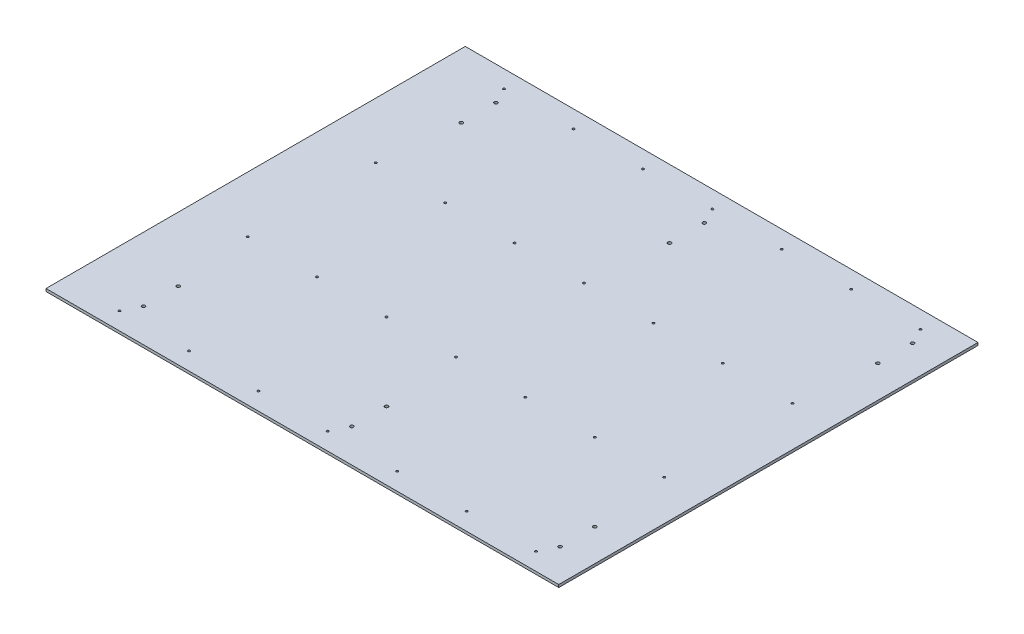
SolidWorks part; units mm, degrees
material "PC High Viscosity"
ref_plane "Front Plane" through (0, 0, 0) normal (0, 0, 1) x (1, 0, 0)
ref_plane "Top Plane" through (0, 0, 0) normal (0, 1, 0) x (1, 0, 0)
ref_plane "Right Plane" through (0, 0, 0) normal (1, 0, 0) x (0, 0, -1)
sketch "Sketch1" plane through (0, 0, 0) normal (0, 1, 0) x (1, 0, 0)
  line L1 (609.6, -498.475) -> (-609.6, -498.475)
  line L2 (609.6, -498.475) -> (609.6, 498.475)
  line L3 (609.6, 498.475) -> (-609.6, 498.475)
  line L4 (-609.6, -498.475) -> (-609.6, 498.475)
  line L5 (609.6, -498.475) -> (-609.6, 498.475) construction
  line L6 (609.6, 498.475) -> (-609.6, -498.475) construction
  point P0 (0, 0)
  dimension "D1" = 1219.2
  dimension "D2" = 996.95
extrude "Boss-Extrude1" add sketch "Sketch1" along normal blind 6.35
hole_wizard "13/64 (0.20313) Diameter Hole1" positions "Sketch2" profile "Sketch3" hole size "13/64" standard "ANSI Inch" end condition through all
sketch "Sketch2" plane through (0, 6.35, 0) normal (0, 1, 0) x (1, 0, 0)
  line L1 (-609.6, -498.475) -> (609.6, -498.475) construction
  line L2 (609.6, -498.475) -> (609.6, 498.475) construction
  point P0 (514.35, -457.2)
  dimension "D1" = 95.25
  dimension "D2" = 41.275
sketch "Sketch3" plane through (514.35, 6.35, 457.2) normal (1, 0, 0) x (0, 0, 1)
  line L0 (0, 0) -> (0, 6.35)
  line L1 (0, 6.35) -> (2.5798, 6.35)
  line L2 (2.5798, 6.35) -> (2.5798, 0)
  line L5 (2.5798, 0) -> (0, 0)
  line L11 (0, -6.35) -> (0, 107.95) construction
  dimension "Thru Hole Dia." = 5.1595
  dimension "Thru Hole Depth" = 6.35
pattern_linear "LPattern1" count 4 spacing 304.8 along (0, 0, -1) count 7 spacing 165.1 along (-1, 0, 0) of "13/64 (0.20313) Diameter Hole1"
sketch "Sketch4" plane through (0, 6.35, 0) normal (0, 1, 0) x (1, 0, 0)
  line L0 (609.6, 498.475) -> (-609.6, 498.475) construction
  line L1 (609.6, -498.475) -> (609.6, 498.475) construction
  circle A2 centre (533.4, 419.1) radius 3.9687
  circle A3 centre (533.4, 336.55) radius 3.9687
  dimension "D1" = 7.9375
  dimension "D4" = 82.55
  dimension "D2" = 79.375
  dimension "D3" = 76.2
extrude "Cut-Extrude1" cut sketch "Sketch4" against normal through all
mirror "Mirror1" about plane through (0, 0, 0) normal (0, 0, 1) of "Cut-Extrude1"
pattern_linear "LPattern2" count 3 spacing 495.3 along (-1, 0, 0) of "Cut-Extrude1", "Mirror1"
